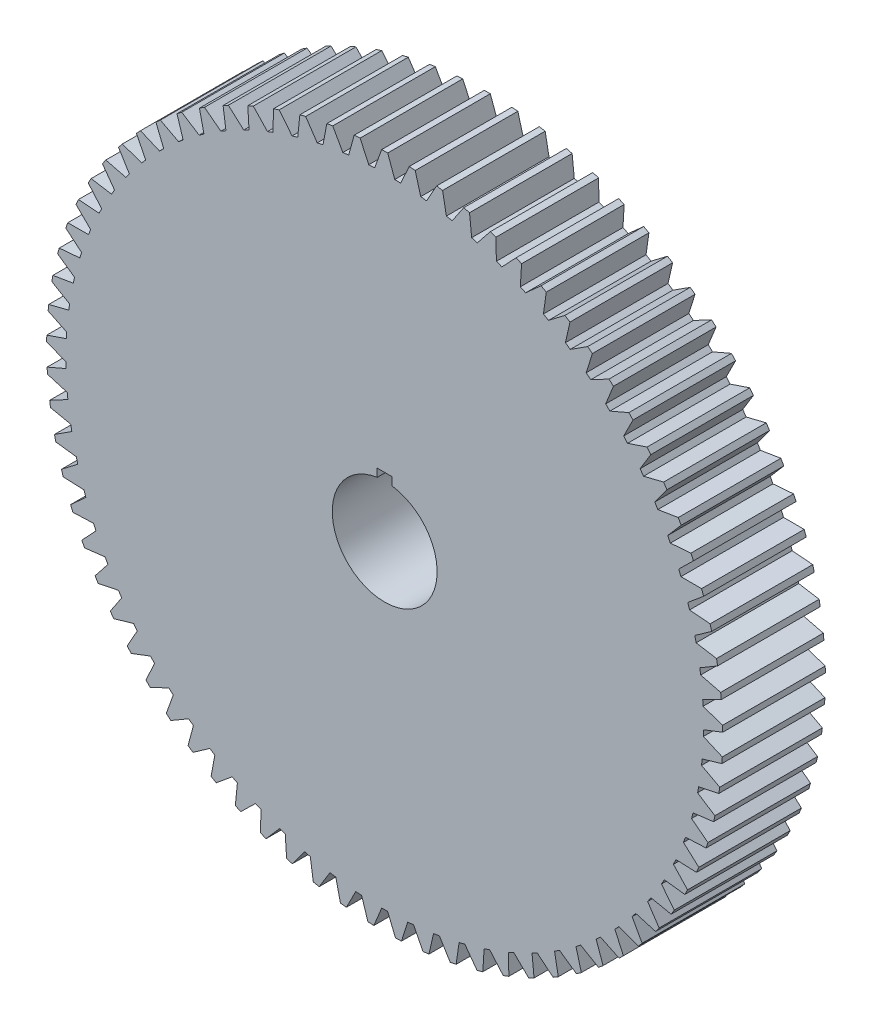
SolidWorks part; units mm, degrees
ref_plane "Front Plane" through (0, 0, 0) normal (0, 0, 1) x (1, 0, 0)
ref_plane "Top Plane" through (0, 0, 0) normal (0, 1, 0) x (1, 0, 0)
ref_plane "Right Plane" through (0, 0, 0) normal (1, 0, 0) x (0, 0, -1)
sketch "Sketch2" plane through (0, 0, 0) normal (0, 0, 1) x (1, 0, 0)
  line L0 (1.27, 143.3266) -> (4.2647, 135.0988)
  line L1 (-1.27, 143.3266) -> (-4.2647, 135.0988)
  line L2 (0, 19.05) -> (0, 143.3322) construction
  line L3 (12.9482, 142.7461) -> (15.2623, 134.3017)
  line L4 (10.4167, 142.9532) -> (6.7613, 134.9969)
  line L5 (24.5403, 141.2158) -> (26.1583, 132.6108)
  line L6 (22.034, 141.6285) -> (17.7423, 133.9966)
  line L7 (35.969, 138.7456) -> (36.8803, 130.0374)
  line L8 (33.5047, 139.3612) -> (28.6053, 132.1046)
  line L9 (47.1584, 135.3522) -> (47.3568, 126.5986)
  line L10 (44.7525, 136.1666) -> (39.2778, 129.3334)
  line L11 (58.0339, 131.0579) -> (57.5182, 122.3173)
  line L12 (55.7024, 132.0657) -> (49.689, 125.7015)
  line L13 (68.5233, 125.8915) -> (67.2968, 117.2221)
  line L14 (66.2817, 127.086) -> (59.7695, 121.2332)
  line L15 (78.5566, 119.8874) -> (76.6276, 111.3467)
  line L16 (76.4198, 121.2606) -> (69.4523, 115.958)
  line L17 (88.0671, 113.0854) -> (85.4484, 104.7303)
  line L18 (86.0494, 114.6282) -> (78.6728, 109.9112)
  line L19 (96.9916, 105.5308) -> (93.7006, 97.417)
  line L20 (95.1063, 107.233) -> (87.3698, 103.1329)
  line L21 (105.2706, 97.2739) -> (101.3292, 89.4554)
  line L22 (103.5304, 99.1241) -> (95.4854, 95.6682)
  line L23 (112.8491, 88.3697) -> (108.2835, 80.8985)
  line L24 (111.2654, 90.3556) -> (102.9655, 87.567)
  line L25 (119.6765, 78.8774) -> (114.5171, 71.8032)
  line L26 (118.26, 80.9858) -> (109.7604, 78.883)
  line L27 (125.7075, 68.8602) -> (119.9887, 62.2301)
  line L28 (124.4676, 71.077) -> (115.8249, 69.674)
  line L29 (130.902, 58.3848) -> (124.6618, 52.2428)
  line L30 (129.8469, 60.6952) -> (121.1186, 60.0013)
  line L31 (135.2253, 47.5208) -> (128.5053, 41.9079)
  line L32 (134.362, 49.9096) -> (125.6062, 49.9294)
  line L33 (138.6488, 36.3405) -> (131.4936, 31.2941)
  line L34 (137.983, 38.7917) -> (129.258, 39.5252)
  line L35 (141.1495, 24.9185) -> (133.6068, 20.472)
  line L36 (140.6858, 27.4158) -> (132.0496, 28.858)
  line L37 (142.711, 13.3305) -> (134.8309, 9.5137)
  line L38 (142.4523, 15.8573) -> (133.9624, 17.9987)
  line L39 (143.3227, 1.6539) -> (135.1577, -1.508)
  line L40 (143.2708, 4.1934) -> (134.9837, 7.0196)
  line L41 (142.9806, -10.0337) -> (134.585, -12.5195)
  line L42 (143.1359, -7.4985) -> (135.1067, -4.0062)
  line L43 (141.687, -21.6546) -> (133.1168, -23.4478)
  line L44 (142.0485, -19.1404) -> (134.3306, -15.0053)
  line L45 (139.4505, -33.1313) -> (130.7626, -34.2201)
  line L46 (140.0157, -30.655) -> (132.6606, -25.9046)
  line L47 (136.286, -44.3876) -> (127.5383, -44.7646)
  line L48 (137.0511, -41.9656) -> (130.1077, -36.6314)
  line L49 (132.2145, -55.3485) -> (123.4652, -55.0112)
  line L50 (133.1745, -52.9969) -> (126.689, -47.1145)
  line L51 (127.2631, -65.941) -> (118.5704, -64.8917)
  line L52 (128.4116, -63.6755) -> (122.4271, -57.2841)
  line L53 (121.4649, -76.0947) -> (112.8866, -74.3403)
  line L54 (122.7942, -73.9304) -> (117.3506, -67.0724)
  line L55 (114.8583, -85.742) -> (106.4516, -83.2943)
  line L56 (116.3596, -83.6932) -> (111.4931, -76.4144)
  line L57 (107.4873, -94.8187) -> (99.3081, -91.6939)
  line L58 (109.1507, -92.8991) -> (104.8936, -85.2479)
  line L59 (99.4011, -103.2645) -> (91.5038, -99.4833)
  line L60 (101.2153, -101.4868) -> (97.5961, -93.514)
  line L61 (90.6533, -111.023) -> (83.0905, -106.6107)
  line L62 (92.6064, -109.3991) -> (89.6491, -101.1579)
  line L63 (81.3023, -118.0426) -> (74.1242, -113.0286)
  line L64 (83.3812, -116.5834) -> (81.1055, -108.1285)
  line L65 (71.4102, -124.2767) -> (64.6647, -118.6944)
  line L66 (73.6012, -122.9918) -> (72.0221, -114.3796)
  line L67 (61.0428, -129.6838) -> (54.7748, -123.5702)
  line L68 (63.3313, -128.5817) -> (62.4595, -119.8695)
  line L69 (50.2693, -134.2279) -> (44.5205, -127.6237)
  line L70 (52.64, -133.316) -> (52.4812, -124.5616)
  line L71 (39.1612, -137.8786) -> (33.9698, -130.8278)
  line L72 (41.5983, -137.163) -> (42.1536, -128.4249)
  line L73 (27.7925, -140.6119) -> (23.1931, -133.1614)
  line L74 (30.2798, -140.0973) -> (31.5456, -131.4335)
  line L75 (16.2389, -142.4093) -> (12.262, -134.6088)
  line L76 (18.7599, -142.0992) -> (20.7276, -133.5674)
  line L77 (4.5771, -143.2591) -> (1.2494, -135.1603)
  line L78 (7.115, -143.1555) -> (9.7716, -134.8124)
  line L79 (-7.115, -143.1555) -> (-9.7716, -134.8124)
  line L80 (-4.5771, -143.2591) -> (-1.2494, -135.1603)
  line L81 (-18.7599, -142.0992) -> (-20.7276, -133.5674)
  line L82 (-16.2389, -142.4093) -> (-12.262, -134.6088)
  line L83 (-30.2798, -140.0973) -> (-31.5456, -131.4335)
  line L84 (-27.7925, -140.6119) -> (-23.1931, -133.1614)
  line L85 (-41.5983, -137.163) -> (-42.1536, -128.4249)
  line L86 (-39.1612, -137.8786) -> (-33.9698, -130.8278)
  line L87 (-52.64, -133.316) -> (-52.4812, -124.5616)
  line L88 (-50.2693, -134.2279) -> (-44.5205, -127.6237)
  line L89 (-63.3313, -128.5817) -> (-62.4595, -119.8695)
  line L90 (-61.0428, -129.6838) -> (-54.7748, -123.5702)
  line L91 (-73.6012, -122.9918) -> (-72.0221, -114.3796)
  line L92 (-71.4102, -124.2767) -> (-64.6647, -118.6944)
  line L93 (-83.3812, -116.5834) -> (-81.1055, -108.1285)
  line L94 (-81.3023, -118.0426) -> (-74.1242, -113.0286)
  line L95 (-92.6064, -109.3991) -> (-89.6491, -101.1579)
  line L96 (-90.6533, -111.023) -> (-83.0905, -106.6107)
  line L97 (-101.2153, -101.4868) -> (-97.5961, -93.514)
  line L98 (-99.4011, -103.2645) -> (-91.5038, -99.4833)
  line L99 (-109.1507, -92.8991) -> (-104.8936, -85.2479)
  line L100 (-107.4873, -94.8187) -> (-99.3081, -91.6939)
  line L101 (-116.3596, -83.6932) -> (-111.4931, -76.4144)
  line L102 (-114.8583, -85.742) -> (-106.4516, -83.2943)
  line L103 (-122.7942, -73.9304) -> (-117.3506, -67.0724)
  line L104 (-121.4649, -76.0947) -> (-112.8866, -74.3403)
  line L105 (-128.4116, -63.6755) -> (-122.4271, -57.2841)
  line L106 (-127.2631, -65.941) -> (-118.5704, -64.8917)
  line L107 (-133.1745, -52.9969) -> (-126.689, -47.1145)
  line L108 (-132.2145, -55.3485) -> (-123.4652, -55.0112)
  line L109 (-137.0511, -41.9656) -> (-130.1077, -36.6314)
  line L110 (-136.286, -44.3876) -> (-127.5383, -44.7646)
  line L111 (-140.0157, -30.655) -> (-132.6606, -25.9046)
  line L112 (-139.4505, -33.1313) -> (-130.7626, -34.2201)
  line L113 (-142.0485, -19.1404) -> (-134.3306, -15.0053)
  line L114 (-141.687, -21.6546) -> (-133.1168, -23.4478)
  line L115 (-143.1359, -7.4985) -> (-135.1067, -4.0062)
  line L116 (-142.9806, -10.0337) -> (-134.585, -12.5195)
  line L117 (-143.2708, 4.1934) -> (-134.9837, 7.0196)
  line L118 (-143.3227, 1.6539) -> (-135.1577, -1.508)
  line L119 (-142.4523, 15.8573) -> (-133.9624, 17.9987)
  line L120 (-142.711, 13.3305) -> (-134.8309, 9.5137)
  line L121 (-140.6858, 27.4158) -> (-132.0496, 28.858)
  line L122 (-141.1495, 24.9185) -> (-133.6068, 20.472)
  line L123 (-137.983, 38.7917) -> (-129.258, 39.5252)
  line L124 (-138.6488, 36.3405) -> (-131.4936, 31.2941)
  line L125 (-134.362, 49.9096) -> (-125.6062, 49.9294)
  line L126 (-135.2253, 47.5208) -> (-128.5053, 41.9079)
  line L127 (-129.8469, 60.6952) -> (-121.1186, 60.0013)
  line L128 (-130.902, 58.3848) -> (-124.6618, 52.2428)
  line L129 (-124.4676, 71.077) -> (-115.8249, 69.674)
  line L130 (-125.7075, 68.8602) -> (-119.9887, 62.2301)
  line L131 (-118.26, 80.9858) -> (-109.7604, 78.883)
  line L132 (-119.6765, 78.8774) -> (-114.5171, 71.8032)
  line L133 (-111.2654, 90.3556) -> (-102.9655, 87.567)
  line L134 (-112.8491, 88.3697) -> (-108.2835, 80.8985)
  line L135 (-103.5304, 99.1241) -> (-95.4854, 95.6682)
  line L136 (-105.2706, 97.2739) -> (-101.3292, 89.4554)
  line L137 (-95.1063, 107.233) -> (-87.3698, 103.1329)
  line L138 (-96.9916, 105.5308) -> (-93.7006, 97.417)
  line L139 (-86.0494, 114.6282) -> (-78.6728, 109.9112)
  line L140 (-88.0671, 113.0854) -> (-85.4484, 104.7303)
  line L141 (-76.4198, 121.2606) -> (-69.4523, 115.958)
  line L142 (-78.5566, 119.8874) -> (-76.6276, 111.3467)
  line L143 (-66.2817, 127.086) -> (-59.7695, 121.2332)
  line L144 (-68.5233, 125.8915) -> (-67.2968, 117.2221)
  line L145 (-55.7024, 132.0657) -> (-49.689, 125.7015)
  line L146 (-58.0339, 131.0579) -> (-57.5182, 122.3173)
  line L147 (-44.7525, 136.1666) -> (-39.2778, 129.3334)
  line L148 (-47.1584, 135.3522) -> (-47.3568, 126.5986)
  line L149 (-33.5047, 139.3612) -> (-28.6053, 132.1046)
  line L150 (-35.969, 138.7456) -> (-36.8803, 130.0374)
  line L151 (-22.034, 141.6285) -> (-17.7423, 133.9966)
  line L152 (-24.5403, 141.2158) -> (-26.1583, 132.6108)
  line L153 (-10.4167, 142.9532) -> (-6.7613, 134.9969)
  line L154 (-12.9482, 142.7461) -> (-15.2623, 134.3017)
  line L156 (0, 25.4) -> (-3.175, 25.4)
  line L157 (-3.175, 25.4) -> (-3.175, 21.997)
  line L158 (0, 25.4) -> (3.175, 25.4)
  line L159 (3.175, 25.4) -> (3.175, 21.997)
  arc A1 (1.27, 143.3266) -> (-1.27, 143.3266) centre (0, 0) ccw
  arc A3 (12.9482, 142.7461) -> (10.4167, 142.9532) centre (0, 0) ccw
  arc A5 (24.5403, 141.2158) -> (22.034, 141.6285) centre (0, 0) ccw
  arc A7 (35.969, 138.7456) -> (33.5047, 139.3612) centre (0, 0) ccw
  arc A9 (47.1584, 135.3522) -> (44.7525, 136.1666) centre (0, 0) ccw
  arc A11 (58.0339, 131.0579) -> (55.7024, 132.0657) centre (0, 0) ccw
  arc A13 (68.5233, 125.8915) -> (66.2817, 127.086) centre (0, 0) ccw
  arc A15 (78.5566, 119.8874) -> (76.4198, 121.2606) centre (0, 0) ccw
  arc A17 (88.0671, 113.0854) -> (86.0494, 114.6282) centre (0, 0) ccw
  arc A19 (96.9916, 105.5308) -> (95.1063, 107.233) centre (0, 0) ccw
  arc A21 (105.2706, 97.2739) -> (103.5304, 99.1241) centre (0, 0) ccw
  arc A23 (112.8491, 88.3697) -> (111.2654, 90.3556) centre (0, 0) ccw
  arc A25 (119.6765, 78.8774) -> (118.26, 80.9858) centre (0, 0) ccw
  arc A27 (125.7075, 68.8602) -> (124.4676, 71.077) centre (0, 0) ccw
  arc A29 (130.902, 58.3848) -> (129.8469, 60.6952) centre (0, 0) ccw
  arc A31 (135.2253, 47.5208) -> (134.362, 49.9096) centre (0, 0) ccw
  arc A33 (138.6488, 36.3405) -> (137.983, 38.7917) centre (0, 0) ccw
  arc A35 (141.1495, 24.9185) -> (140.6858, 27.4158) centre (0, 0) ccw
  arc A37 (142.711, 13.3305) -> (142.4523, 15.8573) centre (0, 0) ccw
  arc A39 (143.3227, 1.6539) -> (143.2708, 4.1934) centre (0, 0) ccw
  arc A41 (142.9806, -10.0337) -> (143.1359, -7.4985) centre (0, 0) ccw
  arc A43 (141.687, -21.6546) -> (142.0485, -19.1404) centre (0, 0) ccw
  arc A45 (139.4505, -33.1313) -> (140.0157, -30.655) centre (0, 0) ccw
  arc A47 (136.286, -44.3876) -> (137.0511, -41.9656) centre (0, 0) ccw
  arc A49 (132.2145, -55.3485) -> (133.1745, -52.9969) centre (0, 0) ccw
  arc A51 (127.2631, -65.941) -> (128.4116, -63.6755) centre (0, 0) ccw
  arc A53 (121.4649, -76.0947) -> (122.7942, -73.9304) centre (0, 0) ccw
  arc A55 (114.8583, -85.742) -> (116.3596, -83.6932) centre (0, 0) ccw
  arc A57 (107.4873, -94.8187) -> (109.1507, -92.8991) centre (0, 0) ccw
  arc A59 (99.4011, -103.2645) -> (101.2153, -101.4868) centre (0, 0) ccw
  arc A61 (90.6533, -111.023) -> (92.6064, -109.3991) centre (0, 0) ccw
  arc A63 (81.3023, -118.0426) -> (83.3812, -116.5834) centre (0, 0) ccw
  arc A65 (71.4102, -124.2767) -> (73.6012, -122.9918) centre (0, 0) ccw
  arc A67 (61.0428, -129.6838) -> (63.3313, -128.5817) centre (0, 0) ccw
  arc A69 (50.2693, -134.2279) -> (52.64, -133.316) centre (0, 0) ccw
  arc A71 (39.1612, -137.8786) -> (41.5983, -137.163) centre (0, 0) ccw
  arc A73 (27.7925, -140.6119) -> (30.2798, -140.0973) centre (0, 0) ccw
  arc A75 (16.2389, -142.4093) -> (18.7599, -142.0992) centre (0, 0) ccw
  arc A77 (4.5771, -143.2591) -> (7.115, -143.1555) centre (0, 0) ccw
  arc A79 (-7.115, -143.1555) -> (-4.5771, -143.2591) centre (0, 0) ccw
  arc A81 (-18.7599, -142.0992) -> (-16.2389, -142.4093) centre (0, 0) ccw
  arc A83 (-30.2798, -140.0973) -> (-27.7925, -140.6119) centre (0, 0) ccw
  arc A85 (-41.5983, -137.163) -> (-39.1612, -137.8786) centre (0, 0) ccw
  arc A87 (-52.64, -133.316) -> (-50.2693, -134.2279) centre (0, 0) ccw
  arc A89 (-63.3313, -128.5817) -> (-61.0428, -129.6838) centre (0, 0) ccw
  arc A91 (-73.6012, -122.9918) -> (-71.4102, -124.2767) centre (0, 0) ccw
  arc A93 (-83.3812, -116.5834) -> (-81.3023, -118.0426) centre (0, 0) ccw
  arc A95 (-92.6064, -109.3991) -> (-90.6533, -111.023) centre (0, 0) ccw
  arc A97 (-101.2153, -101.4868) -> (-99.4011, -103.2645) centre (0, 0) ccw
  arc A99 (-109.1507, -92.8991) -> (-107.4873, -94.8187) centre (0, 0) ccw
  arc A101 (-116.3596, -83.6932) -> (-114.8583, -85.742) centre (0, 0) ccw
  arc A103 (-122.7942, -73.9304) -> (-121.4649, -76.0947) centre (0, 0) ccw
  arc A105 (-128.4116, -63.6755) -> (-127.2631, -65.941) centre (0, 0) ccw
  arc A107 (-133.1745, -52.9969) -> (-132.2145, -55.3485) centre (0, 0) ccw
  arc A109 (-137.0511, -41.9656) -> (-136.286, -44.3876) centre (0, 0) ccw
  arc A111 (-140.0157, -30.655) -> (-139.4505, -33.1313) centre (0, 0) ccw
  arc A113 (-142.0485, -19.1404) -> (-141.687, -21.6546) centre (0, 0) ccw
  arc A115 (-143.1359, -7.4985) -> (-142.9806, -10.0337) centre (0, 0) ccw
  arc A117 (-143.2708, 4.1934) -> (-143.3227, 1.6539) centre (0, 0) ccw
  arc A119 (-142.4523, 15.8573) -> (-142.711, 13.3305) centre (0, 0) ccw
  arc A121 (-140.6858, 27.4158) -> (-141.1495, 24.9185) centre (0, 0) ccw
  arc A123 (-137.983, 38.7917) -> (-138.6488, 36.3405) centre (0, 0) ccw
  arc A125 (-134.362, 49.9096) -> (-135.2253, 47.5208) centre (0, 0) ccw
  arc A127 (-129.8469, 60.6952) -> (-130.902, 58.3848) centre (0, 0) ccw
  arc A129 (-124.4676, 71.077) -> (-125.7075, 68.8602) centre (0, 0) ccw
  arc A131 (-118.26, 80.9858) -> (-119.6765, 78.8774) centre (0, 0) ccw
  arc A133 (-111.2654, 90.3556) -> (-112.8491, 88.3697) centre (0, 0) ccw
  arc A135 (-103.5304, 99.1241) -> (-105.2706, 97.2739) centre (0, 0) ccw
  arc A137 (-95.1063, 107.233) -> (-96.9916, 105.5308) centre (0, 0) ccw
  arc A139 (-86.0494, 114.6282) -> (-88.0671, 113.0854) centre (0, 0) ccw
  arc A141 (-76.4198, 121.2606) -> (-78.5566, 119.8874) centre (0, 0) ccw
  arc A143 (-66.2817, 127.086) -> (-68.5233, 125.8915) centre (0, 0) ccw
  arc A145 (-55.7024, 132.0657) -> (-58.0339, 131.0579) centre (0, 0) ccw
  arc A147 (-44.7525, 136.1666) -> (-47.1584, 135.3522) centre (0, 0) ccw
  arc A149 (-33.5047, 139.3612) -> (-35.969, 138.7456) centre (0, 0) ccw
  arc A151 (-22.034, 141.6285) -> (-24.5403, 141.2158) centre (0, 0) ccw
  arc A153 (-10.4167, 142.9532) -> (-12.9482, 142.7461) centre (0, 0) ccw
  arc A154 (-26.1583, 132.6108) -> (-28.6053, 132.1046) centre (0, 0) ccw
  arc A155 (-3.175, 21.997) -> (3.175, 21.997) centre (0, 0) ccw
  arc A156 (-15.2623, 134.3017) -> (-17.7423, 133.9966) centre (0, 0) ccw
  arc A158 (-4.2647, 135.0988) -> (-6.7613, 134.9969) centre (0, 0) ccw
  arc A159 (6.7613, 134.9969) -> (4.2647, 135.0988) centre (0, 0) ccw
  arc A160 (17.7423, 133.9966) -> (15.2623, 134.3017) centre (0, 0) ccw
  arc A161 (28.6053, 132.1046) -> (26.1583, 132.6108) centre (0, 0) ccw
  arc A162 (39.2778, 129.3334) -> (36.8803, 130.0374) centre (0, 0) ccw
  arc A163 (49.689, 125.7015) -> (47.3568, 126.5986) centre (0, 0) ccw
  arc A164 (59.7695, 121.2332) -> (57.5182, 122.3173) centre (0, 0) ccw
  arc A165 (69.4523, 115.958) -> (67.2968, 117.2221) centre (0, 0) ccw
  arc A166 (78.6728, 109.9112) -> (76.6276, 111.3467) centre (0, 0) ccw
  arc A167 (87.3698, 103.1329) -> (85.4484, 104.7303) centre (0, 0) ccw
  arc A168 (95.4854, 95.6682) -> (93.7006, 97.417) centre (0, 0) ccw
  arc A169 (102.9655, 87.567) -> (101.3292, 89.4554) centre (0, 0) ccw
  arc A170 (109.7604, 78.883) -> (108.2835, 80.8985) centre (0, 0) ccw
  arc A171 (115.8249, 69.674) -> (114.5171, 71.8032) centre (0, 0) ccw
  arc A172 (121.1186, 60.0013) -> (119.9887, 62.2301) centre (0, 0) ccw
  arc A173 (125.6062, 49.9294) -> (124.6618, 52.2428) centre (0, 0) ccw
  arc A174 (129.258, 39.5252) -> (128.5053, 41.9079) centre (0, 0) ccw
  arc A175 (132.0496, 28.858) -> (131.4936, 31.2941) centre (0, 0) ccw
  arc A176 (133.9624, 17.9987) -> (133.6068, 20.472) centre (0, 0) ccw
  arc A177 (134.9837, 7.0196) -> (134.8309, 9.5137) centre (0, 0) ccw
  arc A178 (135.1067, -4.0062) -> (135.1577, -1.508) centre (0, 0) ccw
  arc A179 (134.3306, -15.0053) -> (134.585, -12.5195) centre (0, 0) ccw
  arc A180 (132.6606, -25.9046) -> (133.1168, -23.4478) centre (0, 0) ccw
  arc A181 (130.1077, -36.6314) -> (130.7626, -34.2201) centre (0, 0) ccw
  arc A182 (126.689, -47.1145) -> (127.5383, -44.7646) centre (0, 0) ccw
  arc A183 (122.4271, -57.2841) -> (123.4652, -55.0112) centre (0, 0) ccw
  arc A184 (117.3506, -67.0724) -> (118.5704, -64.8917) centre (0, 0) ccw
  arc A185 (111.4931, -76.4144) -> (112.8866, -74.3403) centre (0, 0) ccw
  arc A186 (104.8936, -85.2479) -> (106.4516, -83.2943) centre (0, 0) ccw
  arc A187 (97.5961, -93.514) -> (99.3081, -91.6939) centre (0, 0) ccw
  arc A188 (89.6491, -101.1579) -> (91.5038, -99.4833) centre (0, 0) ccw
  arc A189 (81.1055, -108.1285) -> (83.0905, -106.6107) centre (0, 0) ccw
  arc A190 (72.0221, -114.3796) -> (74.1242, -113.0286) centre (0, 0) ccw
  arc A191 (62.4595, -119.8695) -> (64.6647, -118.6944) centre (0, 0) ccw
  arc A192 (52.4812, -124.5616) -> (54.7748, -123.5702) centre (0, 0) ccw
  arc A193 (42.1536, -128.4249) -> (44.5205, -127.6237) centre (0, 0) ccw
  arc A194 (31.5456, -131.4335) -> (33.9698, -130.8278) centre (0, 0) ccw
  arc A195 (20.7276, -133.5674) -> (23.1931, -133.1614) centre (0, 0) ccw
  arc A196 (9.7716, -134.8124) -> (12.262, -134.6088) centre (0, 0) ccw
  arc A197 (-1.2494, -135.1603) -> (1.2494, -135.1603) centre (0, 0) ccw
  arc A198 (-12.262, -134.6088) -> (-9.7716, -134.8124) centre (0, 0) ccw
  arc A199 (-23.1931, -133.1614) -> (-20.7276, -133.5674) centre (0, 0) ccw
  arc A200 (-33.9698, -130.8278) -> (-31.5456, -131.4335) centre (0, 0) ccw
  arc A201 (-44.5205, -127.6237) -> (-42.1536, -128.4249) centre (0, 0) ccw
  arc A202 (-54.7748, -123.5702) -> (-52.4812, -124.5616) centre (0, 0) ccw
  arc A203 (-64.6647, -118.6944) -> (-62.4595, -119.8695) centre (0, 0) ccw
  arc A204 (-74.1242, -113.0286) -> (-72.0221, -114.3796) centre (0, 0) ccw
  arc A205 (-83.0905, -106.6107) -> (-81.1055, -108.1285) centre (0, 0) ccw
  arc A206 (-91.5038, -99.4833) -> (-89.6491, -101.1579) centre (0, 0) ccw
  arc A207 (-99.3081, -91.6939) -> (-97.5961, -93.514) centre (0, 0) ccw
  arc A208 (-112.8866, -74.3403) -> (-111.4931, -76.4144) centre (0, 0) ccw
  arc A209 (-106.4516, -83.2943) -> (-104.8936, -85.2479) centre (0, 0) ccw
  arc A210 (-118.5704, -64.8917) -> (-117.3506, -67.0724) centre (0, 0) ccw
  arc A211 (-123.4652, -55.0112) -> (-122.4271, -57.2841) centre (0, 0) ccw
  arc A212 (-127.5383, -44.7646) -> (-126.689, -47.1145) centre (0, 0) ccw
  arc A213 (-130.7626, -34.2201) -> (-130.1077, -36.6314) centre (0, 0) ccw
  arc A214 (-133.1168, -23.4478) -> (-132.6606, -25.9046) centre (0, 0) ccw
  arc A215 (-134.585, -12.5195) -> (-134.3306, -15.0053) centre (0, 0) ccw
  arc A216 (-135.1577, -1.508) -> (-135.1067, -4.0062) centre (0, 0) ccw
  arc A217 (-134.8309, 9.5137) -> (-134.9837, 7.0196) centre (0, 0) ccw
  arc A218 (-133.6068, 20.472) -> (-133.9624, 17.9987) centre (0, 0) ccw
  arc A219 (-131.4936, 31.2941) -> (-132.0496, 28.858) centre (0, 0) ccw
  arc A220 (-128.5053, 41.9079) -> (-129.258, 39.5252) centre (0, 0) ccw
  arc A221 (-124.6618, 52.2428) -> (-125.6062, 49.9294) centre (0, 0) ccw
  arc A222 (-119.9887, 62.2301) -> (-121.1186, 60.0013) centre (0, 0) ccw
  arc A223 (-114.5171, 71.8032) -> (-115.8249, 69.674) centre (0, 0) ccw
  arc A224 (-108.2835, 80.8985) -> (-109.7604, 78.883) centre (0, 0) ccw
  arc A225 (-101.3292, 89.4554) -> (-102.9655, 87.567) centre (0, 0) ccw
  arc A226 (-93.7006, 97.417) -> (-95.4854, 95.6682) centre (0, 0) ccw
  arc A227 (-85.4484, 104.7303) -> (-87.3698, 103.1329) centre (0, 0) ccw
  arc A228 (-76.6276, 111.3467) -> (-78.6728, 109.9112) centre (0, 0) ccw
  arc A229 (-67.2968, 117.2221) -> (-69.4523, 115.958) centre (0, 0) ccw
  arc A230 (-57.5182, 122.3173) -> (-59.7695, 121.2332) centre (0, 0) ccw
  arc A231 (-47.3568, 126.5986) -> (-49.689, 125.7015) centre (0, 0) ccw
  arc A232 (-36.8803, 130.0374) -> (-39.2778, 129.3334) centre (0, 0) ccw
  point P314 (0, 0)
  dimension "D1" = 44.45
  dimension "D2" = 286.6644
  dimension "D3" = 20
  dimension "D4" = 20
  dimension "D5" = 1.27
  dimension "D6" = 1.27
  dimension "D8" = 25.4
  dimension "D9" = 3.175
  dimension "D10" = 3.175
  dimension "D7" = 77
extrude "Boss-Extrude1" add sketch "Sketch2" along normal blind 43.5102
